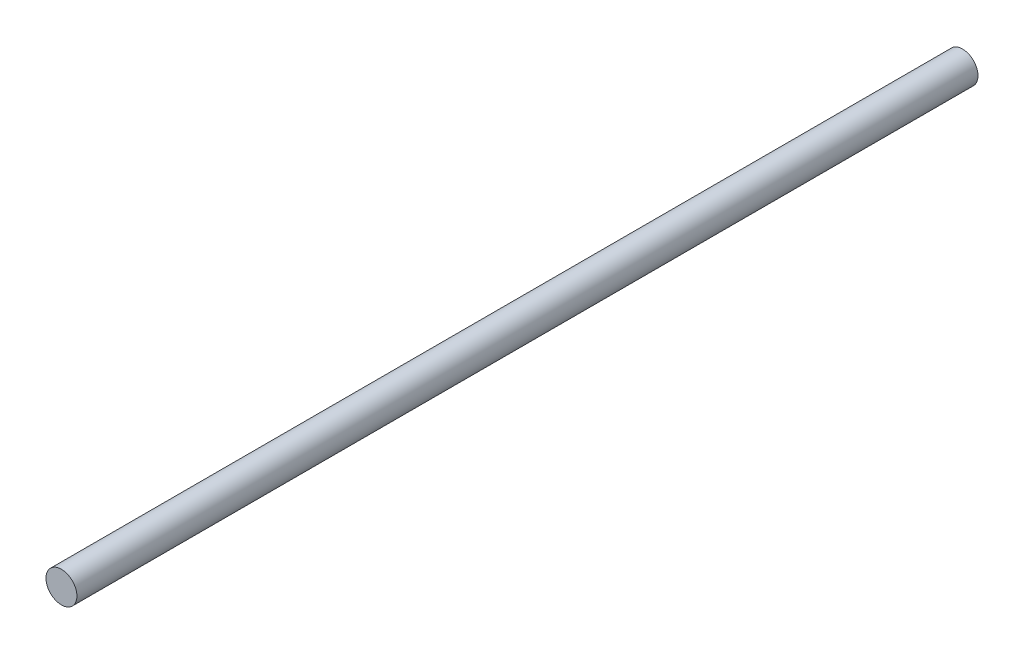
SolidWorks part; units mm, degrees
material "Fibra Carbono"
ref_plane "Alzado" through (0, 0, 0) normal (0, 0, 1) x (1, 0, 0)
ref_plane "Planta" through (0, 0, 0) normal (0, 1, 0) x (1, 0, 0)
ref_plane "Vista lateral" through (0, 0, 0) normal (1, 0, 0) x (0, 0, -1)
sketch "Croquis1" plane through (0, 0, 0) normal (0, 0, 1) x (1, 0, 0)
  circle A0 centre (0, 0) radius 3.5
  dimension "D1" = 7
extrude "Saliente-Extruir1" add sketch "Croquis1" along normal blind 204 contours A0
